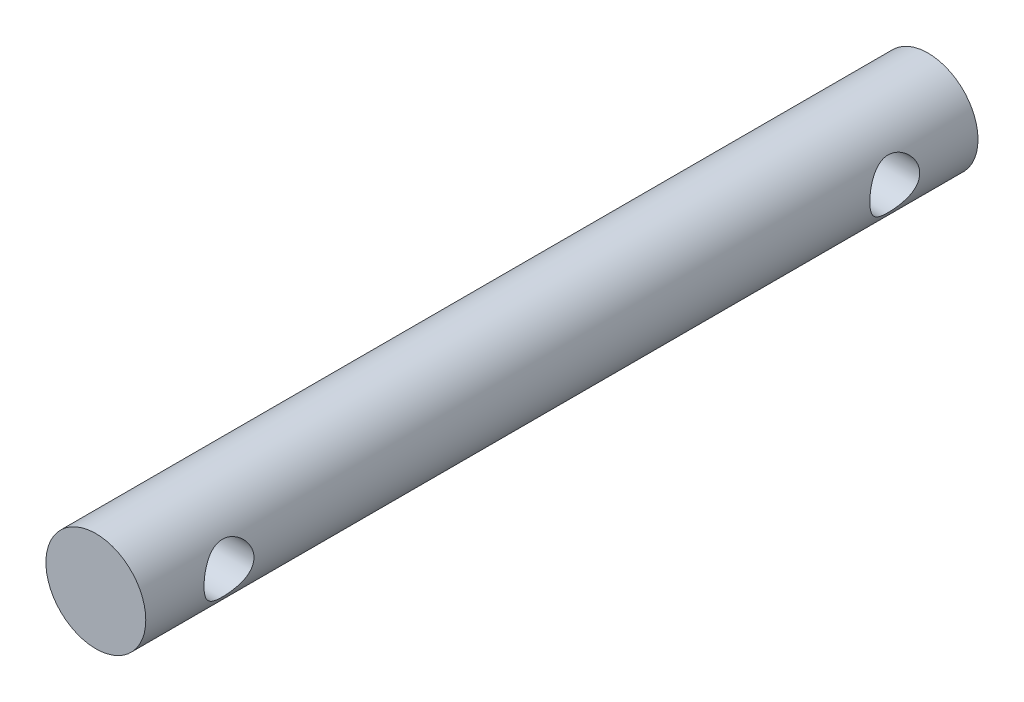
SolidWorks part; units mm, degrees
ref_plane "Front Plane" through (0, 0, 0) normal (0, 0, 1) x (1, 0, 0)
ref_plane "Top Plane" through (0, 0, 0) normal (0, 1, 0) x (1, 0, 0)
ref_plane "Right Plane" through (0, 0, 0) normal (1, 0, 0) x (0, 0, -1)
sketch "Sketch1" plane through (0, 0, 0) normal (0, 0, 1) x (1, 0, 0)
  circle A0 centre (0, 0) radius 3
  dimension "D1" = 6
extrude "Boss-Extrude1" add sketch "Sketch1" along normal blind 50
sketch "Sketch2" plane through (0, 0, 0) normal (1, 0, 0) x (0, 0, -1)
  line L0 (-50, 3) -> (-50, -3) construction
  line L1 (0, -3) -> (0, 3) construction
  circle A0 centre (-45, 0) radius 1.5
  circle A1 centre (-5, 0) radius 1.5
  point P8 (0, 0)
  dimension "D2" = 3
  dimension "D3" = 3
  dimension "D1" = 5
  dimension "D4" = 5
extrude "Cut-Extrude1" cut sketch "Sketch2" against normal through all both and the other way through all
